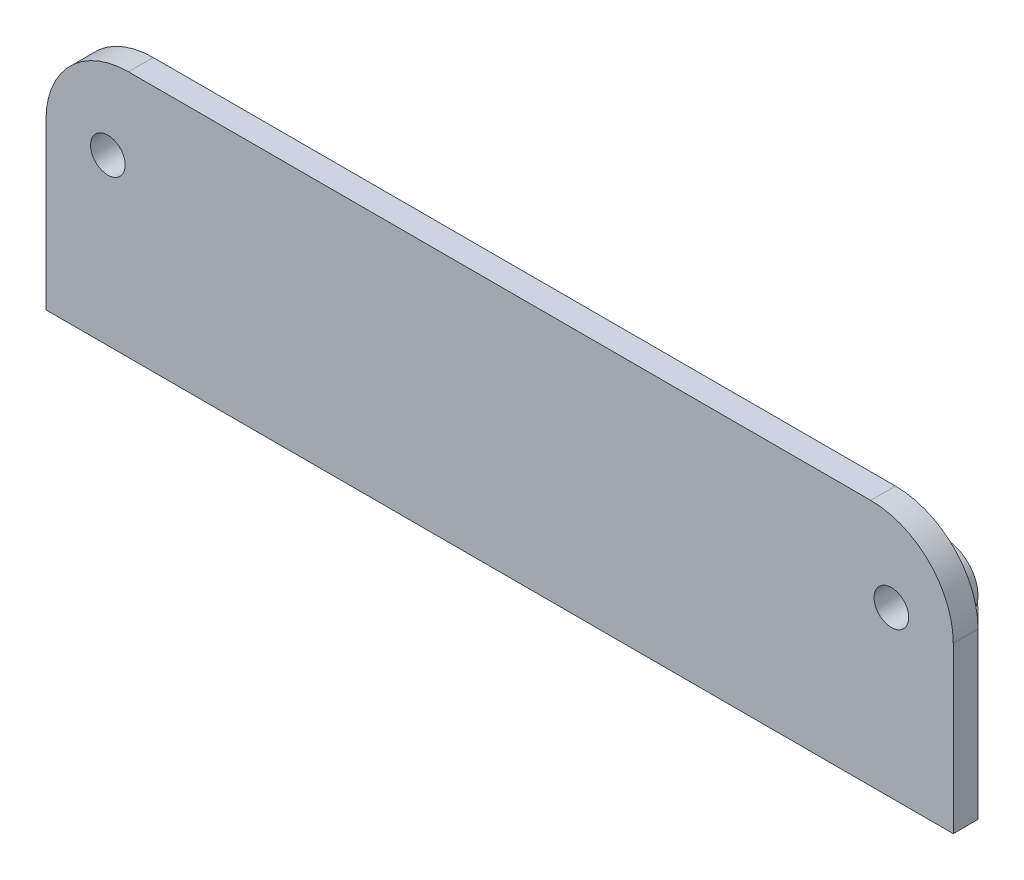
SolidWorks part; units mm, degrees
material "PEI"
ref_plane "Front Plane" through (0, 0, 0) normal (0, 0, 1) x (1, 0, 0)
ref_plane "Top Plane" through (0, 0, 0) normal (0, 1, 0) x (1, 0, 0)
ref_plane "Right Plane" through (0, 0, 0) normal (1, 0, 0) x (0, 0, -1)
sketch "Sketch1" plane through (0, 0, 0) normal (0, 1, 0) x (1, 0, 0)
  line L0 (0, 0) -> (0, -38167.9231) construction
  line L2 (55, -15) -> (-55, -15)
  line L3 (55, -15) -> (55, 15)
  line L4 (55, 15) -> (-55, 15)
  line L5 (-55, -15) -> (-55, 15)
  line L6 (55, -15) -> (-55, 15) construction
  line L7 (55, 15) -> (-55, -15) construction
  circle A0 centre (-20, -6) radius 2.25
  circle A1 centre (20, -6) radius 2.25
  point P3 (0, 0)
  dimension "D3" = 4.5
  dimension "D1" = 30
  dimension "D2" = 110
  dimension "D4" = 21
  dimension "D5" = 20
extrude "Бобышка-Вытянуть1" add sketch "Sketch1" along normal blind 5
sketch "Эскиз1" plane through (0, 0, 15) normal (0, 0, 1) x (1, 0, 0)
  line L1 (-55, 0) -> (55, 0)
  line L2 (-55, 0) -> (-55, 30)
  line L3 (-55, 30) -> (55, 30)
  line L4 (55, 0) -> (55, 30)
  line L5 (55, 5) -> (55, 0) construction
  line L6 (0, 0) -> (0, 50000) construction
  circle A0 centre (-47.5, 20) radius 2.1
  circle A1 centre (47.5, 20) radius 2.1
  dimension "D2" = 4.2
  dimension "D1" = 30
  dimension "D3" = 47.5
  dimension "D4" = 10
extrude "Бобышка-Вытянуть2" add sketch "Эскиз1" along normal blind 3
fillet "Скругление2" radius 10 2 edges at (-55, 30, 16.5) (55, 30, 16.5)
chamfer "Chamfer1" distance 30 angle 45 2 edges at (-55, 2.5, -15) (55, 2.5, -15)
sketch "Эскиз2" plane through (0, 0, 0) normal (1, 0, 0) x (0, 0, -1)
  line L0 (-15, 30) -> (0, 5)
  line L1 (0, 5) -> (-15, 5)
  line L2 (-15, 5) -> (-15, 30)
  line L3 (15, 5) -> (-15, 5) construction
extrude "Бобышка-Вытянуть3" add sketch "Эскиз2" along normal blind 38 and the other way blind 38
sketch "Эскиз3" plane through (0, 5, 0) normal (0, 1, 0) x (1, 0, 0)
  line L0 (0, 0) -> (0, -50000) construction
  line L1 (-38, 0) -> (38, 0) construction
  line L2 (14, 0) -> (26, 0)
  line L3 (14, 0) -> (14, -15)
  line L4 (14, -15) -> (26, -15)
  line L5 (26, 0) -> (26, -15)
  line L6 (-38, -15) -> (38, -15) construction
  line L7 (-26, 0) -> (-26, -15)
  line L8 (-6, 0) -> (6, 0)
  line L9 (-6, 0) -> (-6, -15)
  line L10 (-6, -15) -> (6, -15)
  line L11 (6, 0) -> (6, -15)
  line L12 (-14, -15) -> (-26, -15)
  line L13 (-14, 0) -> (-14, -15)
  line L14 (-14, 0) -> (-26, 0)
  point P15 (0, 0)
  dimension "D1" = 12
  dimension "D2" = 14
  dimension "D3" = 12
extrude "Вырез-Вытянуть1" cut sketch "Эскиз3" along normal through all
fillet "Скругление3" [suppressed] radius 10
sketch "Sketch3" plane through (0, 0, 15) normal (0, 0, -1) x (-1, 0, 0)
  line L0 (0, 0) -> (0, 50000) construction
  circle A0 centre (-47.5, 20) radius 4
  circle A1 centre (-47.5, 20) radius 2.1
  circle A2 centre (47.5, 20) radius 2.1
  circle A3 centre (47.5, 20) radius 4
  dimension "D1" = 8
  dimension "D2" = 4.2
extrude "Boss-Extrude1" add sketch "Sketch3" along normal blind 3.5
sketch "Sketch4" plane through (0, 5, 0) normal (0, 1, 0) x (1, 0, 0)
  line L0 (25, 15) -> (-25, 15) construction
  line L1 (57.2845, 25) -> (-57.2845, 25)
  line L2 (57.2845, 25) -> (57.2845, 5)
  line L3 (57.2845, 5) -> (-57.2845, 5)
  line L4 (-57.2845, 25) -> (-57.2845, 5)
  line L5 (57.2845, 25) -> (-57.2845, 5) construction
  line L6 (57.2845, 5) -> (-57.2845, 25) construction
  point P0 (0, 15)
  dimension "D1" = 10
extrude "Cut-Extrude1" cut sketch "Sketch4" against normal through all
fillet "Fillet1" radius 10 2 edges at (-35, 2.5, -5) (35, 2.5, -5)
